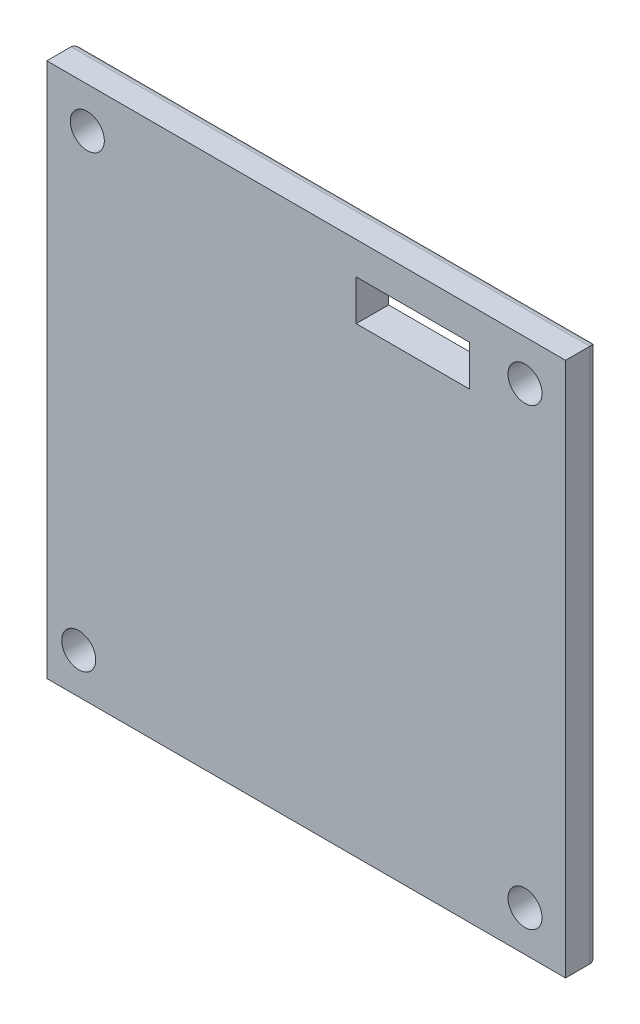
SolidWorks part; units mm, degrees
ref_plane "Front Plane" through (0, 0, 0) normal (0, 0, 1) x (1, 0, 0)
ref_plane "Top Plane" through (0, 0, 0) normal (0, 1, 0) x (1, 0, 0)
ref_plane "Right Plane" through (0, 0, 0) normal (1, 0, 0) x (0, 0, -1)
sketch "Sketch1" plane through (0, 0, 0) normal (0, 0, 1) x (1, 0, 0)
  circle A0 centre (0, 0) radius 21
  dimension "D1" = 42
extrude "Boss-Extrude1" add sketch "Sketch1" along normal blind 8
sketch "Sketch2" plane through (0, 0, 0) normal (0, 0, -1) x (-1, 0, 0)
  circle A0 centre (0, 0) radius 2
extrude "Cut-Extrude1" cut sketch "Sketch2" against normal blind 10 contours A0
sketch "Sketch4" plane through (0, 0, 0) normal (0, 0, -1) x (-1, 0, 0)
  circle A0 centre (16, 0) radius 1.1
  dimension "D1" = 16
  dimension "D3" = 2.2
  dimension "D2" = 0
sketch "Sketch5" plane through (0, 0, 0) normal (0, 0, -1) x (-1, 0, 0)
  circle A0 centre (-16, 0) radius 1.1
  dimension "D1" = 16
  dimension "D3" = 2.2
  dimension "D2" = 32
extrude "Cut-Extrude2" cut sketch "Sketch4" against normal blind 10
extrude "Cut-Extrude3" cut sketch "Sketch5" against normal blind 10
sketch "Sketch11" plane through (0, 0, 0) normal (0, 0, -1) x (-1, 0, 0)
  line L1 (-32, 33) -> (32, 33)
  line L2 (-32, 33) -> (-32, -33)
  line L3 (-32, -33) -> (32, -33)
  line L4 (32, 33) -> (32, -33)
  line L5 (-32, 33) -> (32, -33) construction
  line L6 (-32, -33) -> (32, 33) construction
  point P0 (0, 0)
  dimension "D1" = 64
  dimension "D2" = 66
extrude "Boss-Extrude3" add sketch "Sketch11" along normal blind 4
fillet "Fillet12" radius 1 4 edges at (0, -33, -4) (32, 0, -4) (0, 33, -4) (-32, 0, -4)
sketch "Sketch16" plane through (0, 0, -4) normal (0, 0, -1) x (-1, 0, 0)
  line L0 (31, 32) -> (-31, 32) construction
  line L1 (-20.1709, 29) -> (-6.1709, 29)
  line L2 (-20.1709, 29) -> (-20.1709, 24)
  line L3 (-20.1709, 24) -> (-6.1709, 24)
  line L4 (-6.1709, 29) -> (-6.1709, 24)
  line L5 (-20.1709, 29) -> (-6.1709, 24) construction
  line L6 (-20.1709, 24) -> (-6.1709, 29) construction
  line L7 (-31, 32) -> (-31, -32) construction
  point P0 (-13.1709, 26.5)
  point P7 (-6.1709, 26.5)
  dimension "D1" = 3
  dimension "D2" = 14
  dimension "D3" = 5
  dimension "D4" = 10.8291
extrude "Cut-Extrude7" cut sketch "Sketch16" against normal blind 22
sketch "Sketch17" plane through (0, 0, 8) normal (0, 0, 1) x (1, 0, 0)
  circle A0 centre (0, 0) radius 21
extrude "Cut-Extrude9" cut sketch "Sketch17" against normal blind 8
sketch "Sketch18" plane through (0, 0, -4) normal (0, 0, -1) x (-1, 0, 0)
  line L0 (-32, 33) -> (32, 33) construction
  line L1 (32, -33) -> (-32, -33) construction
  line L2 (32, 33) -> (32, -33) construction
  line L3 (-32, -33) -> (-32, 33) construction
  circle A0 centre (-27, 28) radius 2.1
  circle A1 centre (-27, -28) radius 2.1
  circle A2 centre (28.0566, -28) radius 2.1
  circle A3 centre (27, 28) radius 2.1
  dimension "D1" = 4.2
  dimension "D2" = 4.2
  dimension "D3" = 4.2
  dimension "D4" = 4.2
  dimension "D5" = 5
  dimension "D6" = 5
  dimension "D7" = 5
  dimension "D8" = 3.9434
  dimension "D9" = 5
  dimension "D10" = 5
  dimension "D11" = 5
  dimension "D12" = 5
extrude "Cut-Extrude10" cut sketch "Sketch18" against normal blind 12
sketch "Sketch19" plane through (0, 0, -4) normal (0, 0, -1) x (-1, 0, 0)
  circle A0 centre (0, 0) radius 4
extrude "Boss-Extrude4" add sketch "Sketch19" along normal blind 20
sketch "Sketch20" plane through (0, 0, 0) normal (0, 1, 0) x (1, 0, 0)
  line L0 (4, 24) -> (-4, 24) construction
  line L1 (0, 24) -> (-4, 24)
  line L2 (0, 24) -> (0, 28)
  arc A0 (0, 28) -> (-4, 24) centre (0, 24) ccw
  dimension "D2" = 8
  dimension "D1" = 0
revolve "Revolve1" add sketch "Sketch20" angle 360 about L2
equation "\"ˋ\"=4.51731"
